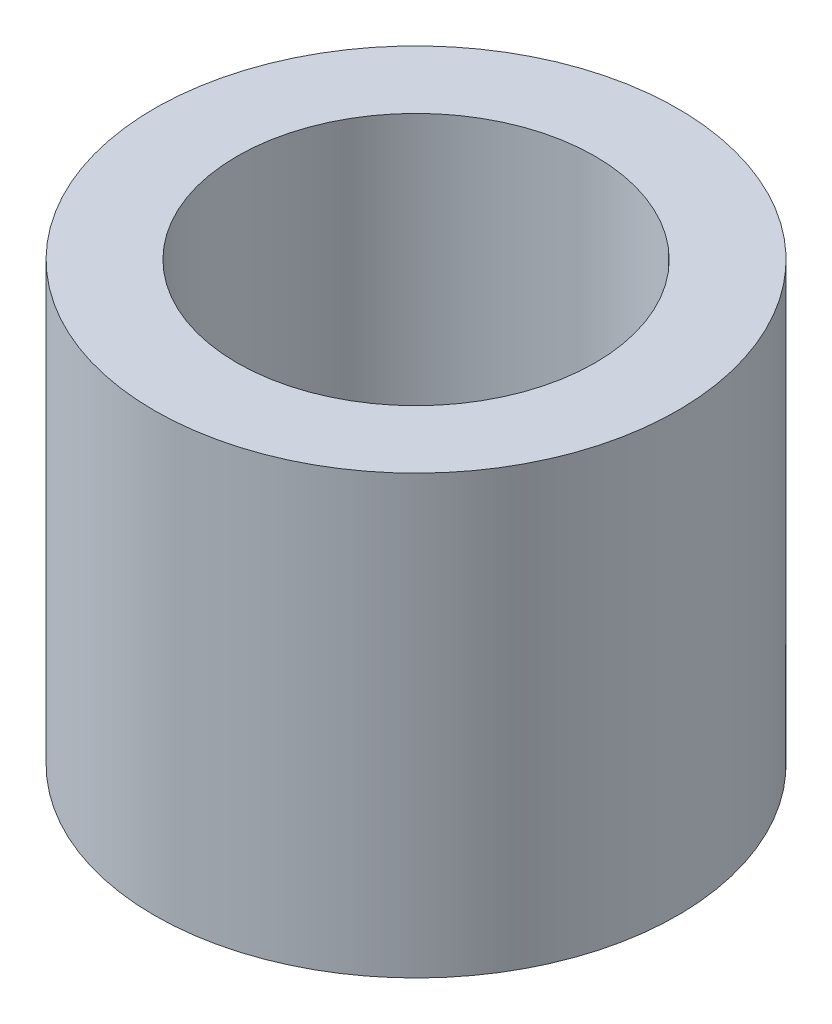
SolidWorks part; units mm, degrees
material "6061-T6 (SS)"
ref_plane "Front" through (0, 0, 0) normal (0, 0, 1) x (1, 0, 0)
ref_plane "Top" through (0, 0, 0) normal (0, 1, 0) x (1, 0, 0)
ref_plane "Right" through (0, 0, 0) normal (1, 0, 0) x (0, 0, -1)
sketch "Sketch1" plane through (0, 0, 0) normal (0, 1, 0) x (1, 0, 0)
  circle A0 centre (0, 0) radius 2.6
  circle A1 centre (0, 0) radius 3.8
  dimension "D1" = 5.2
  dimension "D2" = 1.2
extrude "Boss-Extrude1" add sketch "Sketch1" along normal blind 6.35
